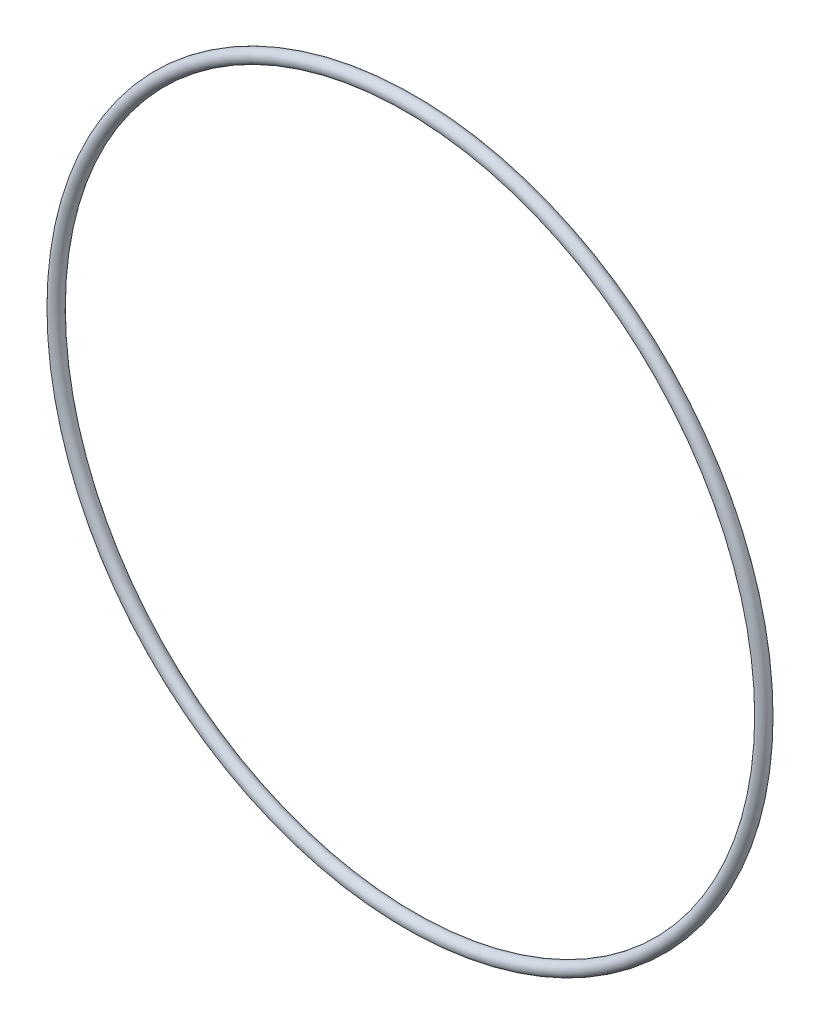
SolidWorks part; units mm, degrees
material "Rubber"
ref_plane "Front" through (0, 0, 0) normal (0, 0, 1) x (1, 0, 0)
ref_plane "Top" through (0, 0, 0) normal (0, 1, 0) x (1, 0, 0)
ref_plane "Right" through (0, 0, 0) normal (1, 0, 0) x (0, 0, -1)
sketch "Sketch1" plane through (0, 0, 0) normal (1, 0, 0) x (0, -1, 0)
  line L0 (0, -0.889) -> (0, 0.889) construction
  line L2 (-54.1896, 0) -> (54.1896, 0) construction
  line L3 (-47.4853, 0) -> (47.4853, 0) construction
  circle A0 centre (48.3743, 0) radius 0.889
  point P9 (47.4853, 0)
  point P10 (49.2633, 0)
  point P13 (48.3743, 0.889)
  point P14 (48.3743, -0.889)
  dimension "Width" = 1.778
  dimension "ID" = 94.9706
revolve "Revolve1" add sketch "Sketch1" angle 360 about L0
